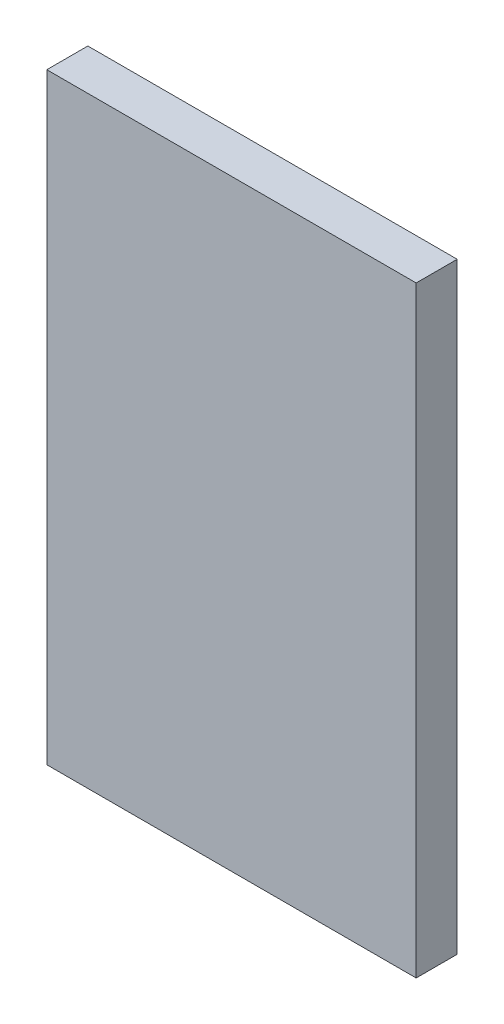
SolidWorks part; units mm, degrees
ref_plane "Plan de face" through (0, 0, 0) normal (0, 0, 1) x (1, 0, 0)
ref_plane "Plan de dessus" through (0, 0, 0) normal (0, 1, 0) x (1, 0, 0)
ref_plane "Plan de droite" through (0, 0, 0) normal (1, 0, 0) x (0, 0, -1)
sketch "Esquisse1" plane through (0, 0, 0) normal (0, 0, 1) x (1, 0, 0)
  line L1 (0, 0) -> (54, 0)
  line L2 (0, 0) -> (0, 88)
  line L3 (0, 88) -> (54, 88)
  line L4 (54, 0) -> (54, 88)
extrude "Extrusion1" add sketch "Esquisse1" along normal blind 6
